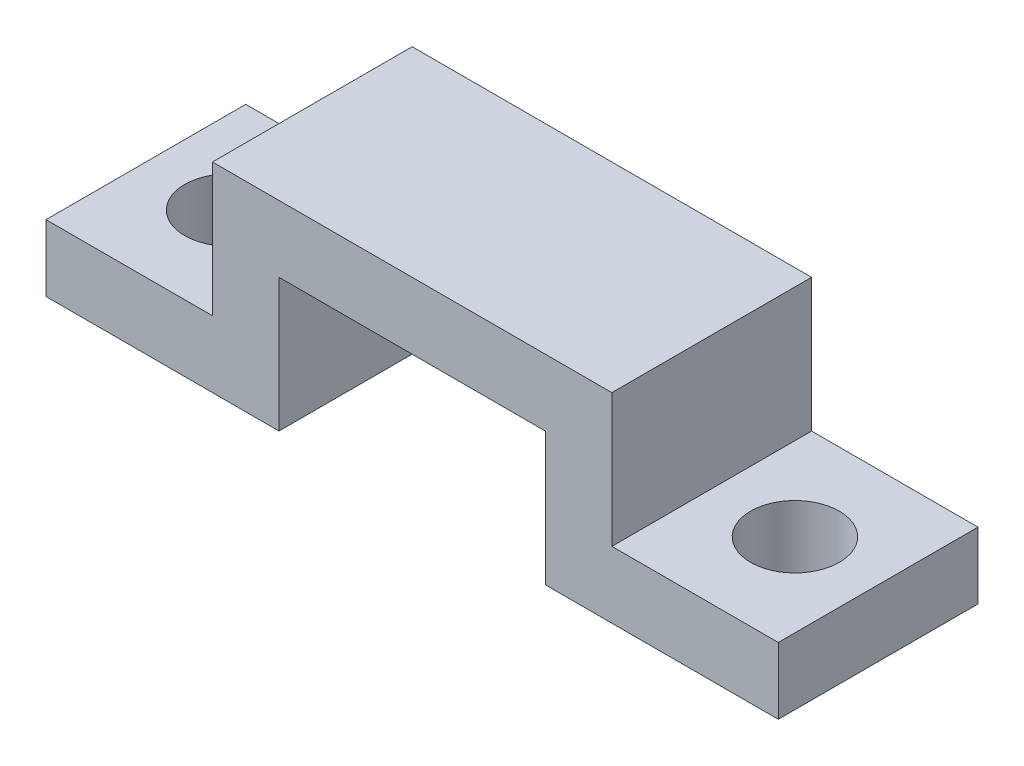
SolidWorks part; units mm, degrees
material "ABS"
ref_plane "Plano frontal" through (0, 0, 0) normal (0, 0, 1) x (1, 0, 0)
ref_plane "Plano superior" through (0, 0, 0) normal (0, 1, 0) x (1, 0, 0)
ref_plane "Plano direito" through (0, 0, 0) normal (1, 0, 0) x (0, 0, -1)
sketch "Esboço1" plane through (0, 0, 0) normal (0, 0, 1) x (1, 0, 0)
  line L0 (0, 0) -> (10.5, 0)
  line L1 (10.5, 0) -> (10.5, 6)
  line L2 (10.5, 6) -> (22.5, 6)
  line L3 (22.5, 6) -> (22.5, 0)
  line L4 (22.5, 0) -> (33, 0)
  line L5 (33, 0) -> (33, 3)
  line L6 (33, 3) -> (25.5, 3)
  line L7 (25.5, 3) -> (25.5, 9)
  line L8 (25.5, 9) -> (7.5, 9)
  line L9 (7.5, 9) -> (7.5, 3)
  line L10 (7.5, 3) -> (0, 3)
  line L11 (0, 3) -> (0, 0)
  dimension "D1" = 12
  dimension "D2" = 3
  dimension "D3" = 3
  dimension "D4" = 3
  dimension "D5" = 6
  dimension "D6" = 3
  dimension "D7" = 3
  dimension "D8" = 10.5
  dimension "D9" = 10.5
extrude "Ressalto-extrusão1" add sketch "Esboço1" along normal blind 9
sketch "Esboço2" plane through (0, 3, 0) normal (0, 1, 0) x (1, 0, 0)
  line L0 (0, -4.5) -> (33, -4.5) construction
  line L1 (0, -9) -> (0, 0) construction
  line L2 (33, -9) -> (33, 0) construction
  circle A0 centre (29.25, -4.5) radius 2
  circle A1 centre (3.75, -4.5) radius 2
  dimension "D3" = 4
  dimension "D4" = 4
  dimension "D1" = 3.75
  dimension "D2" = 3.75
extrude "Corte-extrusão1" cut sketch "Esboço2" against normal blind 10
